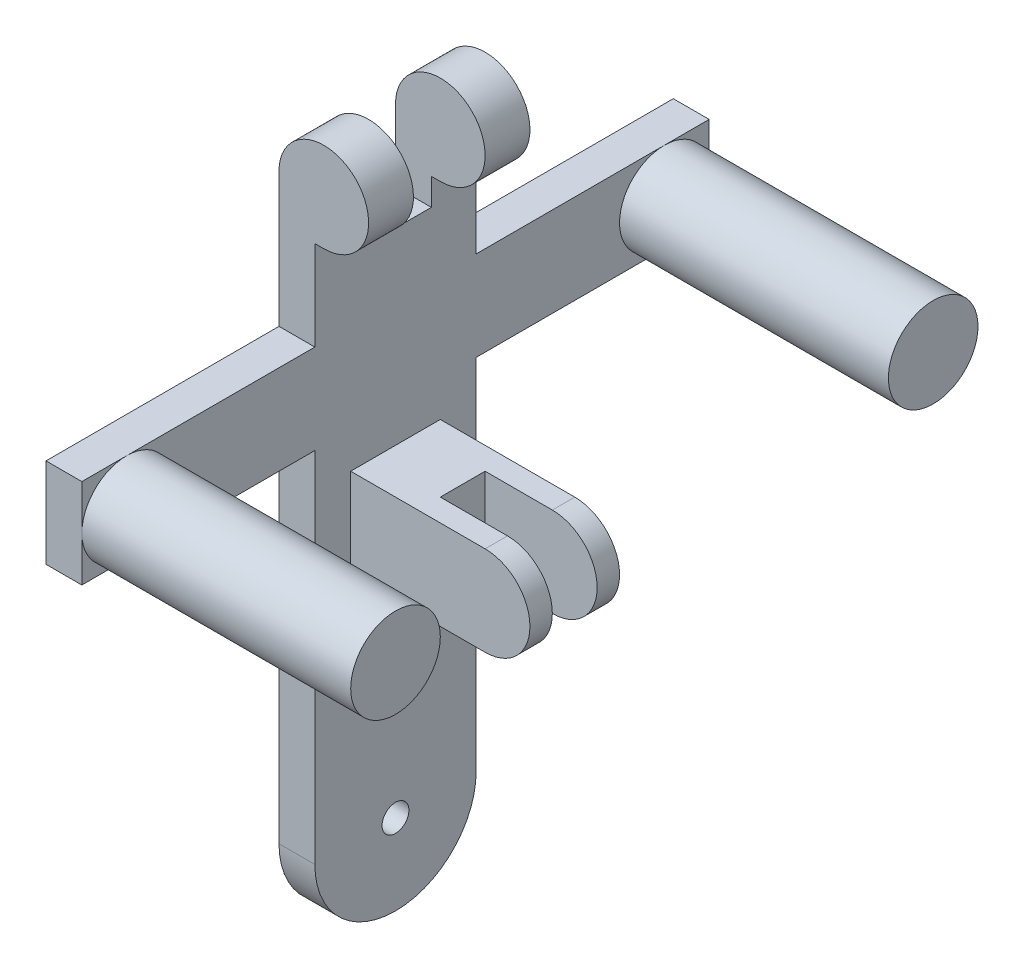
SolidWorks part; units mm, degrees
ref_plane "Front" through (0, 0, 0) normal (0, 0, 1) x (1, 0, 0)
ref_plane "Top" through (0, 0, 0) normal (0, 1, 0) x (1, 0, 0)
ref_plane "Right" through (0, 0, 0) normal (1, 0, 0) x (0, 0, -1)
sketch "草图1" plane through (0, 0, 0) normal (1, 0, 0) x (0, 0, -1)
  line L2 (-18, 0) -> (-18, 140)
  line L3 (-18, 140) -> (18, 140)
  line L4 (18, 0) -> (18, 140)
  arc A0 (-18, 0) -> (18, 0) centre (0, 0) ccw
  circle A1 centre (0, 0) radius 3
  dimension "D1" = 140
extrude "凸台-拉伸1" add sketch "草图1" along normal blind 8
sketch "草图3" plane through (0, 0, -18) normal (0, 0, -1) x (-1, 0, 0)
  line L1 (-8, 140) -> (-20, 140)
  line L2 (-8, 140) -> (-8, 120)
  line L3 (-8, 120) -> (-20, 120)
  line L4 (-20, 140) -> (-20, 120)
  dimension "D1" = 12
  dimension "D2" = 20
extrude "凸台-拉伸2" add sketch "草图3" against normal blind 36
sketch "草图8" plane through (8, 0, 0) normal (1, 0, 0) x (0, 0, -1)
  circle A0 centre (-60, 90) radius 10
  circle A1 centre (60, 90) radius 10
extrude "凸台-拉伸4" add sketch "草图8" along normal blind 60
sketch "草图10" plane through (0, 0, 18) normal (0, 0, 1) x (1, 0, 0)
  line L0 (0, 130) -> (-3.8592, 130)
  line L1 (-3.8592, 130) -> (-3.8592, 144.8396)
  line L2 (-3.8592, 144.8396) -> (22.9918, 144.8396)
  line L3 (22.9918, 144.8396) -> (22.9918, 116.8833)
  line L4 (22.9918, 116.8833) -> (10, 116.8833)
  line L5 (10, 116.8833) -> (10, 120)
  arc A0 (10, 120) -> (0, 130) centre (10, 130) ccw
extrude "切除-拉伸1" cut sketch "草图10" against normal through all
sketch "草图12" plane through (0, 0, 0) normal (0, 0, 1) x (1, 0, 0)
  line L1 (8, 100) -> (0, 100)
  line L2 (8, 100) -> (8, 80)
  line L3 (8, 80) -> (0, 80)
  line L4 (0, 100) -> (0, 80)
  dimension "D1" = 20
  dimension "D2" = 8
extrude "凸台-拉伸5" add sketch "草图12" along normal mid plane 140
sketch "草图13" plane through (0, 0, 0) normal (-1, 0, 0) x (0, 0, 1)
  line L0 (0, 0) -> (0, 176.2771) construction
  line L1 (18, 140) -> (-18, 140) construction
  line L3 (-8, 149.2685) -> (8, 149.2685)
  line L4 (-8, 149.2685) -> (-8, 114)
  line L5 (-8, 114) -> (8, 114)
  line L6 (8, 149.2685) -> (8, 114)
  dimension "D1" = 26
  dimension "D2" = 16
  dimension "D3" = 8
extrude "切除-拉伸2" cut sketch "草图13" against normal blind 140
sketch "草图14" plane through (8, 0, 0) normal (1, 0, 0) x (0, 0, -1)
  line L0 (0, 0) -> (0, 128.2685) construction
  line L1 (18, 80) -> (60, 80) construction
  line L2 (-10, 72) -> (10, 72)
  line L3 (-10, 72) -> (-10, 52)
  line L4 (-10, 52) -> (10, 52)
  line L5 (10, 72) -> (10, 52)
  dimension "D1" = 20
  dimension "D2" = 20
  dimension "D3" = 10
  dimension "D4" = 8
extrude "凸台-拉伸6" add sketch "草图14" along normal blind 40
sketch "草图15" plane through (0, 0, -10) normal (0, 0, -1) x (-1, 0, 0)
  line L1 (-38, 72) -> (-54.3513, 72)
  line L3 (-38, 52) -> (-54.3513, 52)
  line L4 (-54.3513, 72) -> (-54.3513, 52)
  arc A0 (-38, 72) -> (-38, 52) centre (-38, 62) ccw
extrude "切除-拉伸3" cut sketch "草图15" against normal blind 40
sketch "草图16" plane through (0, 0, 0) normal (0, 0, 1) x (1, 0, 0)
  line L0 (8, 80) -> (8, 0) construction
  line L1 (23, 74.824) -> (51.5837, 74.824)
  line L2 (23, 74.824) -> (23, 46.2403)
  line L3 (23, 46.2403) -> (51.5837, 46.2403)
  line L4 (51.5837, 74.824) -> (51.5837, 46.2403)
  dimension "D1" = 15
extrude "切除-拉伸4" cut sketch "草图16" against normal mid plane 10
